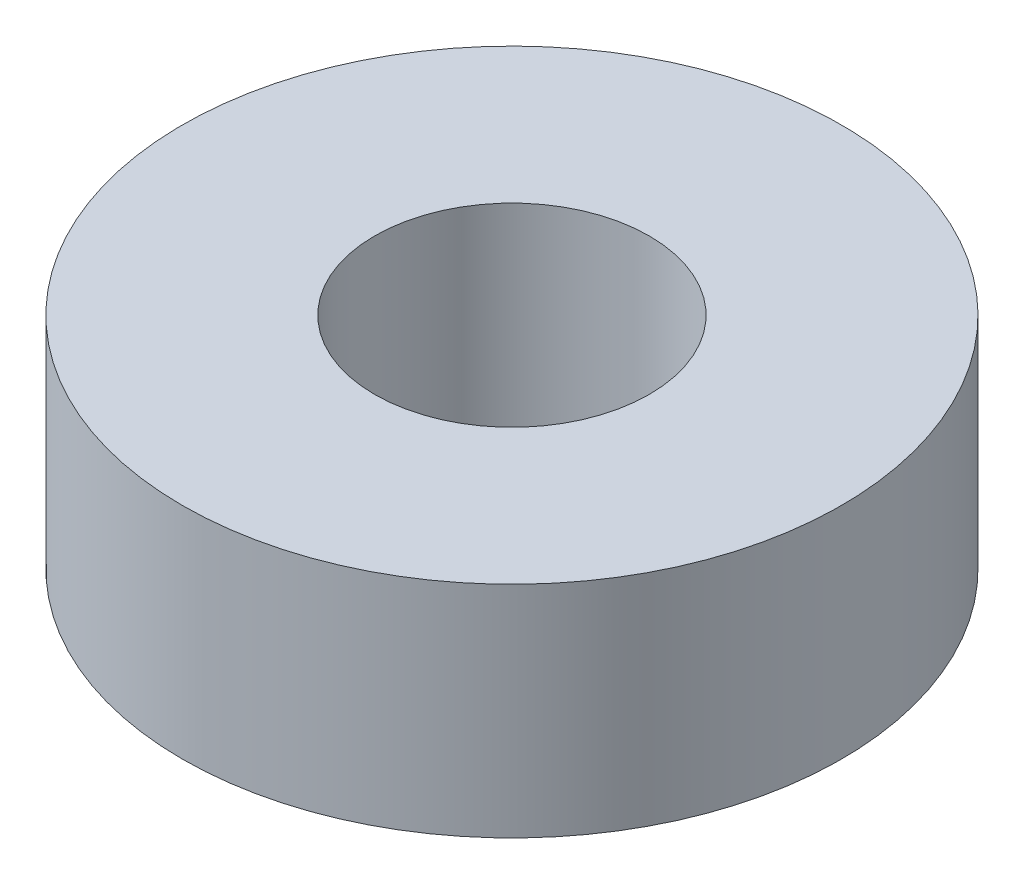
SolidWorks part; units mm, degrees
material "Cast Alloy Steel"
ref_plane "Front Plane" through (0, 0, 0) normal (0, 0, 1) x (1, 0, 0)
ref_plane "Top Plane" through (0, 0, 0) normal (0, 1, 0) x (1, 0, 0)
ref_plane "Right Plane" through (0, 0, 0) normal (1, 0, 0) x (0, 0, -1)
sketch "Sketch1" plane through (0, 0, 0) normal (0, 1, 0) x (1, 0, 0)
  circle A0 centre (0, 0) radius 2.5
  circle A1 centre (0, 0) radius 6
extrude "Boss-Extrude1" add sketch "Sketch1" along normal blind 4
